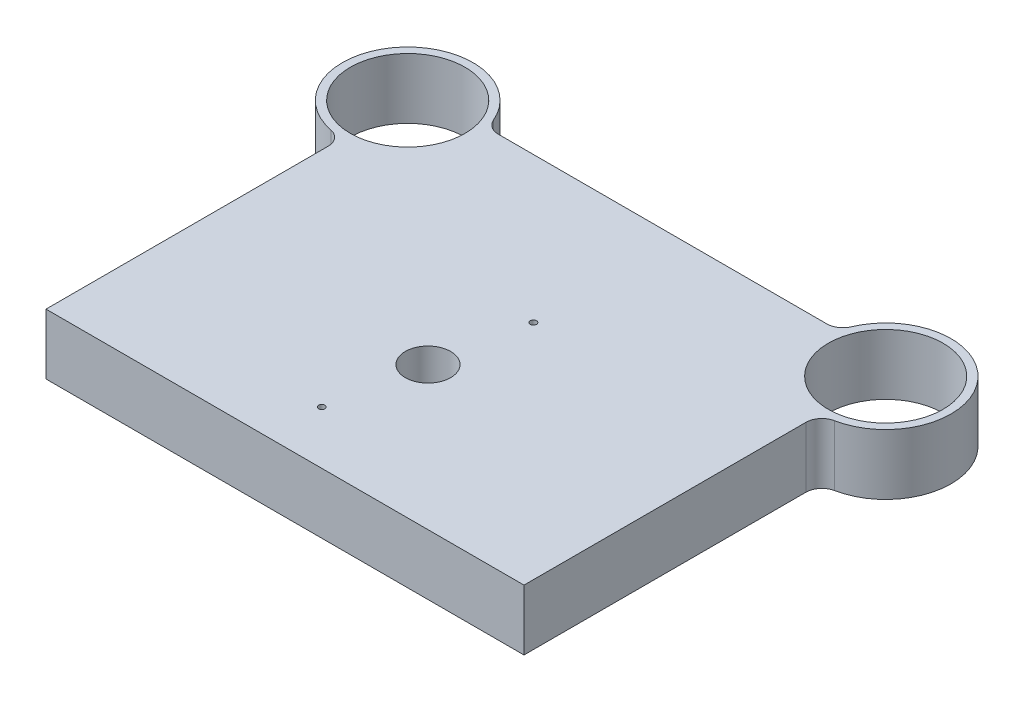
SolidWorks part; units mm, degrees
ref_plane "Front Plane" through (0, 0, 0) normal (0, 0, 1) x (1, 0, 0)
ref_plane "Top Plane" through (0, 0, 0) normal (0, 1, 0) x (1, 0, 0)
ref_plane "Right Plane" through (0, 0, 0) normal (1, 0, 0) x (0, 0, -1)
sketch "Sketch1" plane through (0, 0, 0) normal (0, 1, 0) x (1, 0, 0)
  line L0 (150, 0) -> (-150, 0)
  line L1 (-150, 0) -> (-150, 186)
  line L2 (0, 0) -> (0, 237) construction
  line L3 (110.2382, 237) -> (-110.2382, 237)
  line L4 (150, 0) -> (150, 186)
  arc A0 (-110.2382, 237) -> (-150, 186) centre (-150, 227) ccw
  circle A1 centre (-150, 227) radius 36
  circle A2 centre (150, 227) radius 36
  arc A3 (110.2382, 237) -> (150, 186) centre (150, 227) cw
  dimension "D2" = 82
  dimension "D3" = 72
  dimension "D1" = 227
  dimension "D4" = 300
  dimension "D5" = 300
  dimension "D6" = 237
extrude "Boss-Extrude1" add sketch "Sketch1" along normal blind 38
fillet "Fillet1" radius 10 4 edges at (150, 19, -186) (-150, 19, -186) (110.2382, 19, -237) (-110.2382, 19, -237)
sketch "Sketch2" plane through (0, 38, 0) normal (0, 1, 0) x (1, 0, 0)
  circle A0 centre (-10.25, 33.3) radius 1.99 construction
  circle A1 centre (10.25, 145.68) radius 1.99 construction
  circle A2 centre (-10.25, 33.3) radius 1.99
  circle A3 centre (10.25, 145.68) radius 1.99
extrude "Cut-Extrude1" cut sketch "Sketch2" against normal through all
hole_wizard "M20x1.5 Tapped Hole1" positions "Sketch3" profile "Sketch4" tap size "M20x1.5" standard "DIN"
sketch "Sketch3" plane through (0, 0, 0) normal (0, -1, 0) x (-1, 0, 0)
  point P0 (42.25, 145.68)
  point P3 (-42.25, 145.68)
  point P6 (42.25, 33.3)
  point P9 (-42.25, 33.3)
sketch "Sketch4" plane through (-42.25, 0, -145.68) normal (1, 0, 0) x (0, 0, -1)
  line L0 (0, 0) -> (0, 35.558)
  line L1 (0, 35.558) -> (9.25, 30)
  line L2 (9.25, 30) -> (9.25, 0)
  line L5 (9.25, 0) -> (0, 0)
  line L10 (0, 35.558) -> (-9.25, 30) construction
  line L11 (0, -6.35) -> (0, 107.95) construction
  dimension "Tap Drill Dia." = 18.5
  dimension "Tap Drill Depth" = 30
  dimension "Drill Angle" = 118
cosmetic thread "Hole Thread1" parameters "D1"=25, "D2"=20
cosmetic thread "Hole Thread2" parameters "D1"=25, "D2"=20
cosmetic thread "Hole Thread3" parameters "D1"=25, "D2"=20
cosmetic thread "Hole Thread4" parameters "D1"=25, "D2"=20
sketch "Sketch5" plane through (0, 38, 0) normal (0, 1, 0) x (1, 0, 0)
  line L1 (150, 0) -> (150, 176.99) construction
  line L2 (-150, 0) -> (150, 0) construction
  circle A0 centre (0, 89.74) radius 5
  dimension "D1" = 10
  dimension "D2" = 150
  dimension "D3" = 89.74
hole_wizard "M30x1.5 Tapped Hole1" positions "Sketch8" profile "Sketch9" tap size "M30x1.5" standard "DIN"
sketch "Sketch8" plane through (0, 38, 0) normal (0, 1, 0) x (1, 0, 0)
  point P0 (0, 89.74)
sketch "Sketch9" plane through (0, 38, -89.74) normal (1, 0, 0) x (0, 0, 1)
  line L0 (0, 0) -> (0, 38.5623)
  line L1 (0, 38.5623) -> (14.25, 30)
  line L2 (14.25, 30) -> (14.25, 0)
  line L5 (14.25, 0) -> (0, 0)
  line L10 (0, 38.5623) -> (-14.25, 30) construction
  line L11 (0, -6.35) -> (0, 107.95) construction
  dimension "Tap Drill Dia." = 28.5
  dimension "Tap Drill Depth" = 30
  dimension "Drill Angle" = 118
cosmetic thread "Hole Thread5" parameters "D1"=25, "D2"=30
